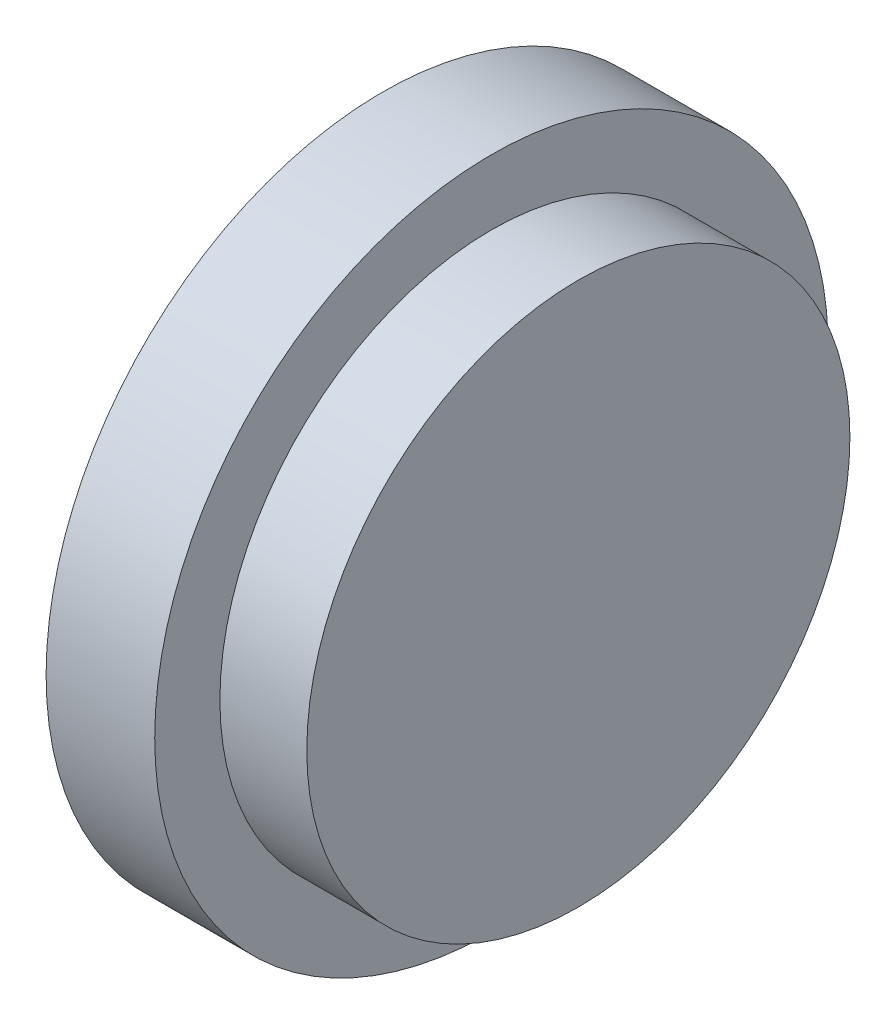
SolidWorks part; units mm, degrees
material "6061-T4 (SS)"
ref_plane "Front Plane" through (0, 0, 0) normal (0, 0, 1) x (1, 0, 0)
ref_plane "Top Plane" through (0, 0, 0) normal (0, 1, 0) x (1, 0, 0)
ref_plane "Right Plane" through (0, 0, 0) normal (1, 0, 0) x (0, 0, -1)
sketch "Sketch1" plane through (0, 0, 0) normal (0, 0, 1) x (1, 0, 0)
  line L0 (0, 0) -> (9, 0) construction
  line L1 (0, 0) -> (0, 15.5)
  line L2 (0, 15.5) -> (5, 15.5)
  line L3 (5, 15.5) -> (5, 12.5)
  line L4 (5, 12.5) -> (9, 12.5)
  line L5 (9, 12.5) -> (9, 0)
  line L6 (0, 0) -> (9, 0)
  dimension "D1" = 5
  dimension "D2" = 15.5
  dimension "D3" = 9
  dimension "D4" = 12.5
revolve "Revolve1" add sketch "Sketch1" angle 360 about L0
